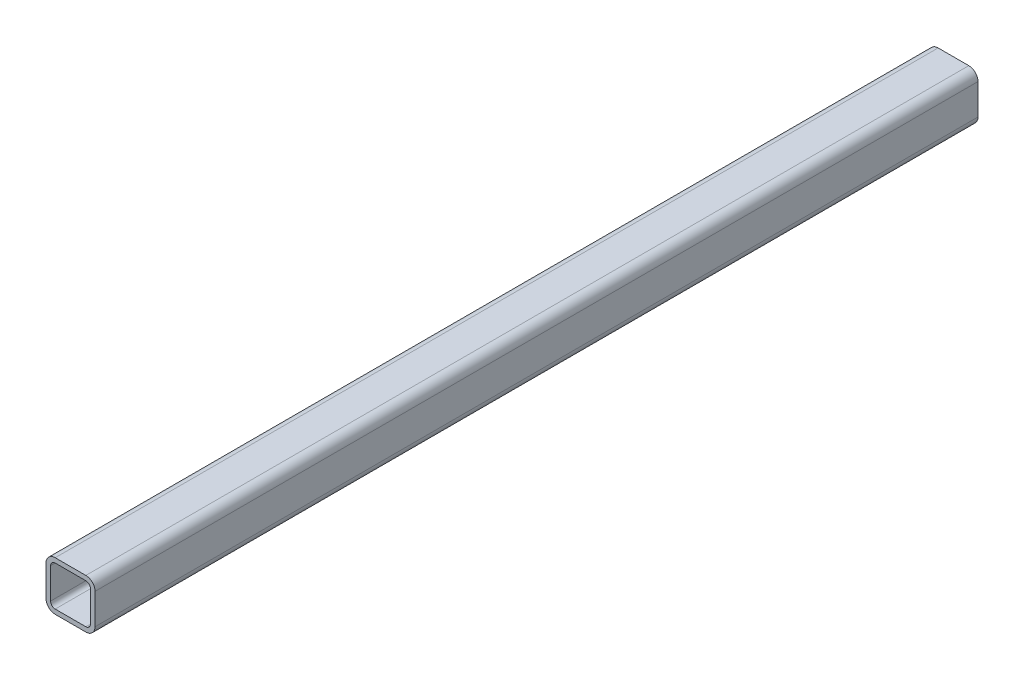
SolidWorks part; units mm, degrees
ref_plane "Plane1" through (0, 0, 0) normal (0, 0, 1) x (1, 0, 0)
ref_plane "Plane2" through (0, 0, 0) normal (0, 1, 0) x (1, 0, 0)
ref_plane "Plane3" through (0, 0, 0) normal (1, 0, 0) x (0, 0, -1)
sketch "Sketch1" plane through (0, 0, 0) normal (0, 0, 1) x (1, 0, 0)
  line L0 (9.525, 4.7625) -> (41.275, 4.7625)
  line L1 (4.7625, 9.525) -> (4.7625, 41.275)
  line L2 (41.275, 46.0375) -> (9.525, 46.0375)
  line L3 (46.0375, 41.275) -> (46.0375, 9.525)
  line L4 (9.525, 0) -> (41.275, 0)
  line L5 (0, 9.525) -> (0, 41.275)
  line L6 (41.275, 50.8) -> (9.525, 50.8)
  line L7 (50.8, 41.275) -> (50.8, 9.525)
  arc A0 (50.8, 41.275) -> (41.275, 50.8) centre (41.275, 41.275) ccw
  arc A1 (41.275, 0) -> (50.8, 9.525) centre (41.275, 9.525) ccw
  arc A2 (0, 9.525) -> (9.525, 0) centre (9.525, 9.525) ccw
  arc A3 (9.525, 50.8) -> (0, 41.275) centre (9.525, 41.275) ccw
  arc A4 (9.525, 46.0375) -> (4.7625, 41.275) centre (9.525, 41.275) ccw
  arc A5 (46.0375, 41.275) -> (41.275, 46.0375) centre (41.275, 41.275) ccw
  arc A6 (41.275, 4.7625) -> (46.0375, 9.525) centre (41.275, 9.525) ccw
  arc A7 (4.7625, 9.525) -> (9.525, 4.7625) centre (9.525, 9.525) ccw
  dimension "D1" = 9.525
  dimension "Thickness" = 4.7625
  dimension "V_leg" = 50.8
  dimension "H_leg" = 50.8
extrude "BaseTubeS" add sketch "Sketch1" along normal mid plane 914.4
equation "\"D1@Sketch1\" = \"Thickness@Sketch1\" * 2"
